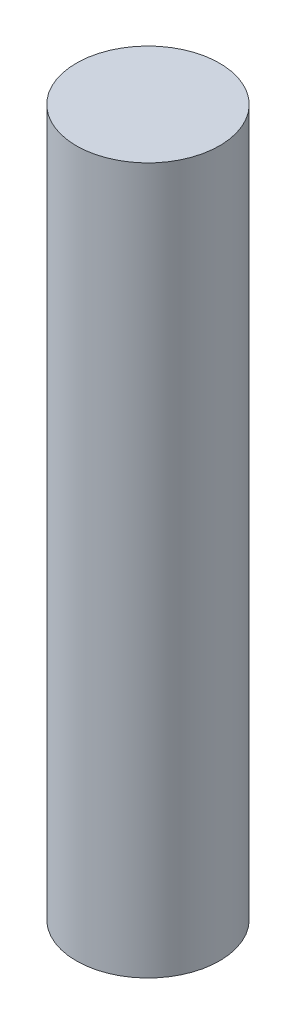
SolidWorks part; units mm, degrees
ref_plane "Alzado" through (0, 0, 0) normal (0, 0, 1) x (1, 0, 0)
ref_plane "Planta" through (0, 0, 0) normal (0, 1, 0) x (1, 0, 0)
ref_plane "Vista lateral" through (0, 0, 0) normal (1, 0, 0) x (0, 0, -1)
sketch "Croquis1" plane through (0, 0, 0) normal (0, 1, 0) x (1, 0, 0)
  circle A0 centre (0, 0) radius 14.2006
extrude "Saliente-Extruir1" add sketch "Croquis1" along normal blind 140
